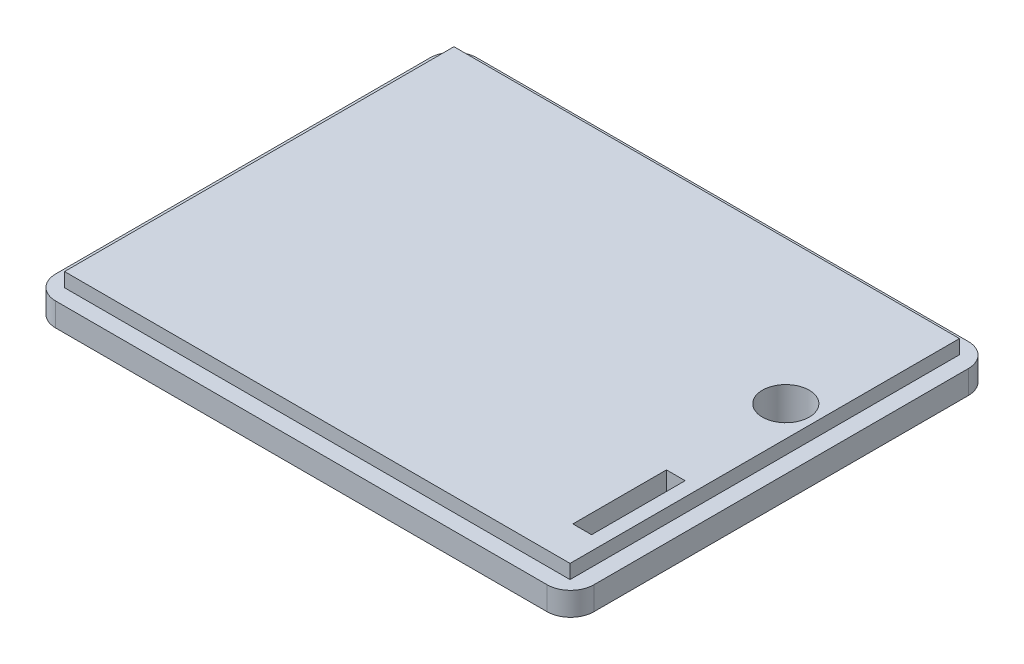
SolidWorks part; units mm, degrees
ref_plane "Front Plane" through (0, 0, 0) normal (0, 0, 1) x (1, 0, 0)
ref_plane "Top Plane" through (0, 0, 0) normal (0, 1, 0) x (1, 0, 0)
ref_plane "Right Plane" through (0, 0, 0) normal (1, 0, 0) x (0, 0, -1)
sketch "Sketch1" plane through (0, 0, 0) normal (0, 1, 0) x (1, 0, 0)
  line L1 (-57.5, 45) -> (57.5, 45)
  line L2 (-57.5, 45) -> (-57.5, -45)
  line L3 (-57.5, -45) -> (57.5, -45)
  line L4 (57.5, 45) -> (57.5, -45)
  line L5 (-57.5, 45) -> (57.5, -45) construction
  line L6 (-57.5, -45) -> (57.5, 45) construction
  point P0 (0, 0)
  dimension "D1" = 115
  dimension "D2" = 90
extrude "Boss-Extrude1" add sketch "Sketch1" along normal blind 5
sketch "Sketch2" plane through (0, 5, 0) normal (0, 1, 0) x (1, 0, 0)
  line L1 (-54, 41.6) -> (54, 41.6)
  line L2 (-54, 41.6) -> (-54, -41.6)
  line L3 (-54, -41.6) -> (54, -41.6)
  line L4 (54, 41.6) -> (54, -41.6)
  line L5 (-54, 41.6) -> (54, -41.6) construction
  line L6 (-54, -41.6) -> (54, 41.6) construction
  point P0 (0, 0)
  dimension "D1" = 108
  dimension "D2" = 83.2
extrude "Boss-Extrude2" add sketch "Sketch2" along normal blind 3
fillet "Fillet1" radius 5 4 edges at (-57.5, 2.5, -45) (57.5, 2.5, -45) (57.5, 2.5, 45) (-57.5, 2.5, 45)
sketch "Sketch3" plane through (0, 0, 0) normal (0, -1, 0) x (-1, 0, 0)
  line L0 (52.5, -45) -> (-52.5, -45) construction
  line L1 (-47, -34) -> (-51, -34)
  line L2 (-47, -34) -> (-47, -14)
  line L3 (-47, -14) -> (-51, -14)
  line L4 (-51, -34) -> (-51, -14)
  line L5 (-57.5, -40) -> (-57.5, 40) construction
  dimension "D1" = 11
  dimension "D2" = 6.5
  dimension "D3" = 4
  dimension "D4" = 20
extrude "Cut-Extrude1" cut sketch "Sketch3" against normal blind 10
fillet "Fillet2" radius 1 4 edges at (49, 0, 14) (51, 0, 24) (47, 0, 24) (49, 0, 34)
sketch "Sketch4" plane through (0, 0, 0) normal (0, -1, 0) x (1, 0, 0)
  line L0 (52.5, -45) -> (-52.5, -45) construction
  line L1 (57.5, 40) -> (57.5, -40) construction
  circle A0 centre (47.5, -11) radius 5
  dimension "D1" = 10
  dimension "D3" = 10
  dimension "D2" = 34
extrude "Cut-Extrude2" cut sketch "Sketch4" against normal blind 10
fillet "Fillet3" radius 1 1 edges at (47.5, 0, -16)
